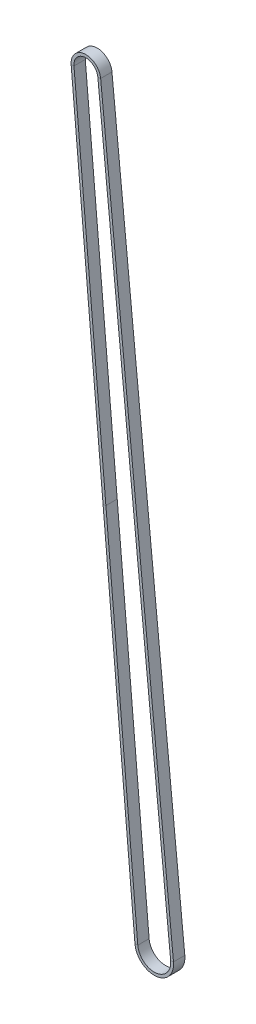
SolidWorks part; units mm, degrees
material "POLYURETHANE (11671)"
ref_plane "Front Plane" through (0, 0, 0) normal (0, 0, 1) x (1, 0, 0)
ref_plane "Top Plane" through (0, 0, 0) normal (0, 1, 0) x (1, 0, 0)
ref_plane "Right Plane" through (0, 0, 0) normal (1, 0, 0) x (0, 0, -1)
sketch "Sketch1" plane through (0, 0, 0) normal (0, 0, 1) x (1, 0, 0)
  line L0 (-42.5298, 385.7613) -> (-8.7167, -0.7625)
  line L1 (-29.8854, 386.9463) -> (8.7066, 0.8703)
  arc A2 (-29.8854, 386.9463) -> (-42.5298, 385.7613) centre (-36.204, 386.3147) ccw
  arc A3 (-8.7167, -0.7625) -> (8.7066, 0.8703) centre (0, 0) ccw
  circle A4 centre (0, 0) radius 8.75 construction
  circle A5 centre (-36.204, 386.3147) radius 6.35 construction
  point P4 (-25.6233, 192.4994)
ref_plane "Plane1" through (-25.6233, 192.4994, 0) normal (0.0871, -0.9962, 0) x (-0.9962, -0.0871, 0)
sketch "Sketch2" plane through (-25.6233, 192.4994, 0) normal (0.0871, -0.9962, 0) x (-0.9962, -0.0871, 0)
  line L1 (1.5, 3) -> (0, 3)
  line L2 (1.5, 3) -> (1.5, -3)
  line L3 (1.5, -3) -> (0, -3)
  line L4 (0, 3) -> (0, -3)
  point P4 (0, 0)
  dimension "D1" = 1.5
  dimension "D2" = 6
sweep "Sweep1" add profiles "Sketch2" path "Sketch1"
